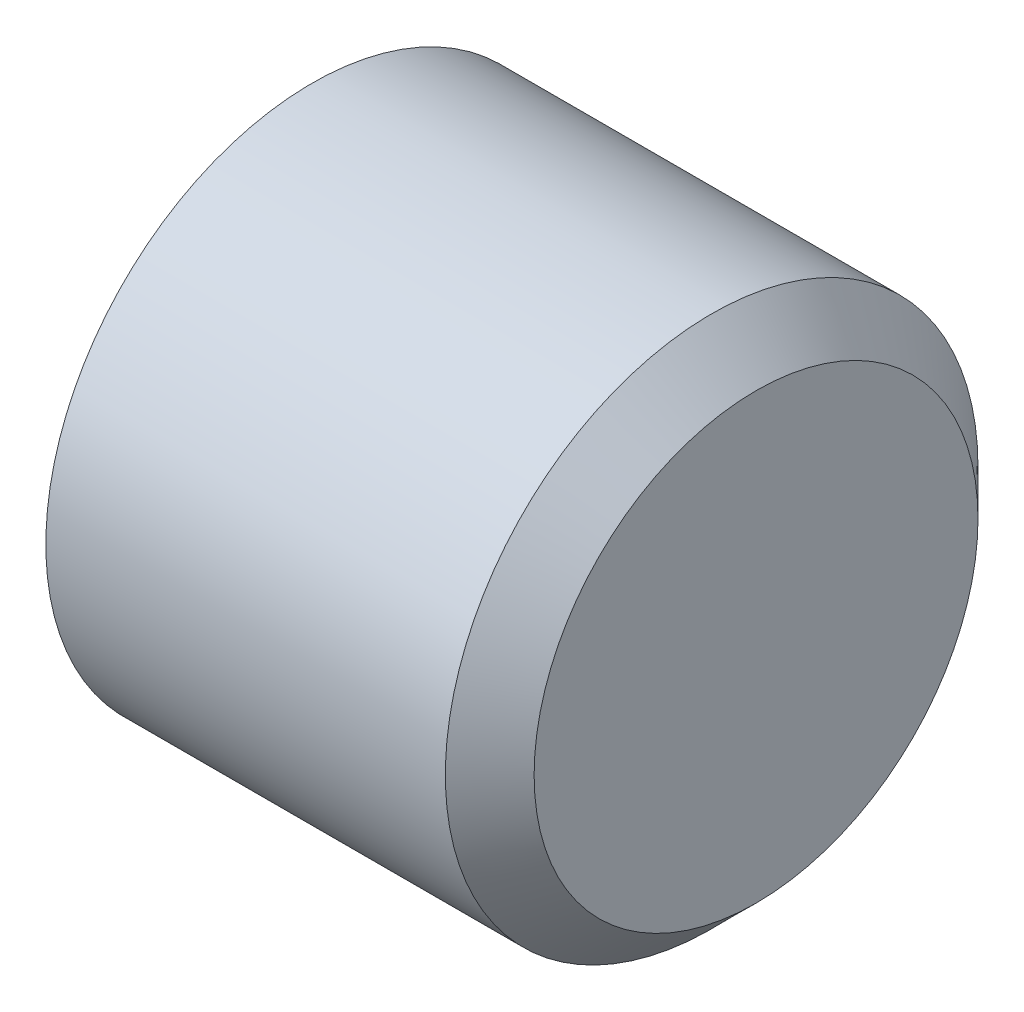
SolidWorks part; units mm, degrees
material "Plain Carbon Steel"
ref_plane "Front Plane" through (0, 0, 0) normal (0, 0, 1) x (1, 0, 0)
ref_plane "Top Plane" through (0, 0, 0) normal (0, 1, 0) x (1, 0, 0)
ref_plane "Right Plane" through (0, 0, 0) normal (1, 0, 0) x (0, 0, -1)
sketch "Sketch1" plane through (0, 0, 0) normal (1, 0, 0) x (0, 0, -1)
  circle A0 centre (0, 0) radius 6
  dimension "D1" = 12
extrude "Boss-Extrude2" add sketch "Sketch1" along normal mid plane 10
hole_wizard "M6x1.0 Tapped Hole1" positions "3DSketch4" profile "Sketch5" tap size "M6x1.0" standard "ANSI Metric"
sketch3d "3DSketch4"
  point P0 (0, 0, 0)
  point P3 (-5, 0, 0)
sketch "Sketch5" plane through (-5, 0, 0) normal (0, 1, 0) x (0, 0, 1)
  line L0 (0, 0) -> (0, 7.5022)
  line L1 (0, 7.5022) -> (2.5, 6)
  line L2 (2.5, 6) -> (2.5, 0)
  line L5 (2.5, 0) -> (0, 0)
  line L10 (0, 7.5022) -> (-2.5, 6) construction
  line L11 (0, -6.35) -> (0, 107.95) construction
  dimension "Tap Drill Dia." = 5
  dimension "Tap Drill Depth" = 6
  dimension "Drill Angle" = 118
cosmetic thread "Hole Thread2" parameters "D1"=6, "D2"=6
cosmetic thread "Hole Thread3" parameters "D1"=6, "D2"=6
chamfer "Chamfer1" distance 1 angle 45 1 edges at (5, 0, -6)
